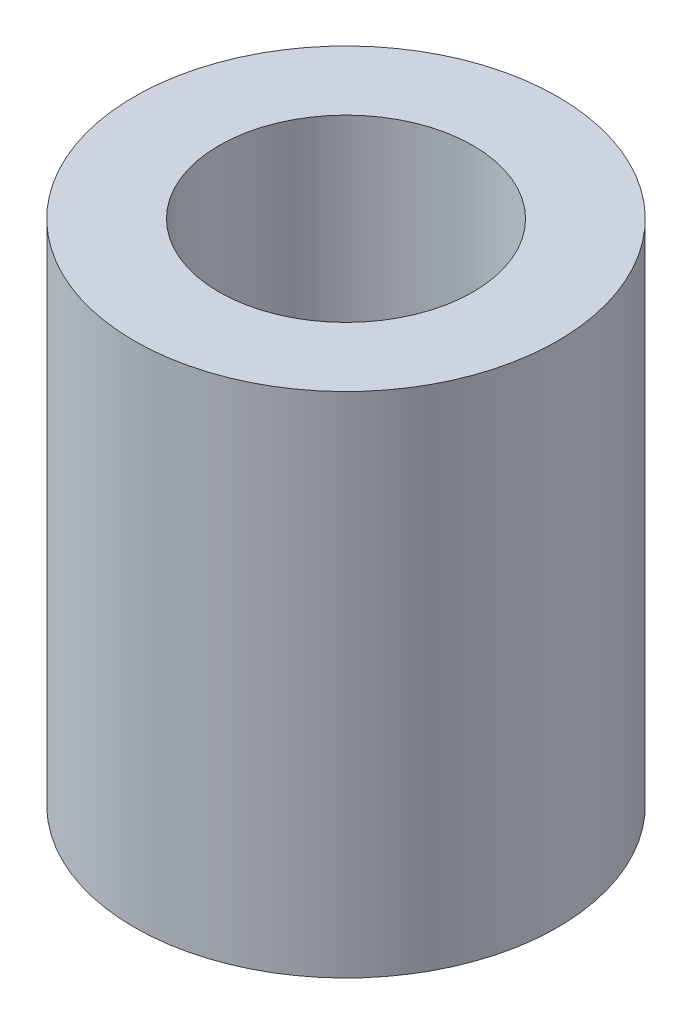
SolidWorks part; units mm, degrees
ref_plane "Front Plane" through (0, 0, 0) normal (0, 0, 1) x (1, 0, 0)
ref_plane "Top Plane" through (0, 0, 0) normal (0, 1, 0) x (1, 0, 0)
ref_plane "Right Plane" through (0, 0, 0) normal (1, 0, 0) x (0, 0, -1)
sketch "Sketch1" plane through (0, 0, 0) normal (0, 1, 0) x (1, 0, 0)
  circle A0 centre (0, 0) radius 2.5
  circle A1 centre (0, 0) radius 1.5
  dimension "D1" = 5
  dimension "D2" = 3
extrude "Boss-Extrude1" add sketch "Sketch1" along normal blind 6
